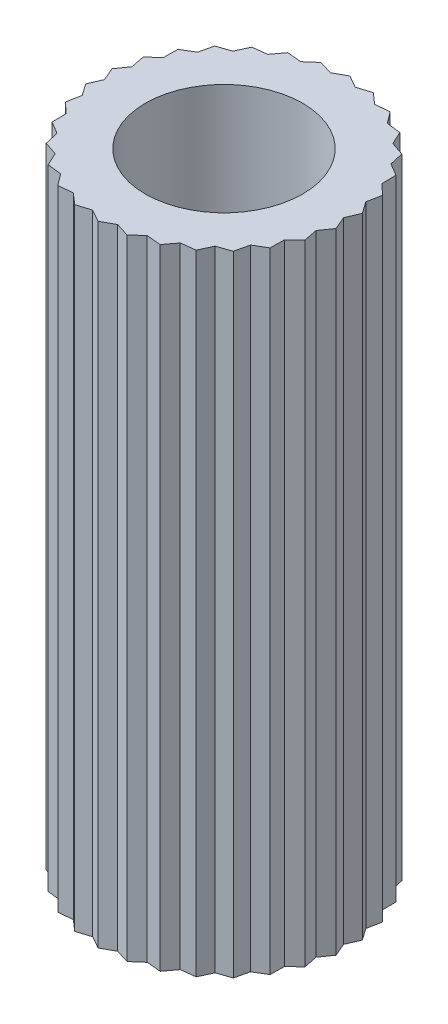
SolidWorks part; units mm, degrees
ref_plane "前视基准面" through (0, 0, 0) normal (0, 0, 1) x (1, 0, 0)
ref_plane "上视基准面" through (0, 0, 0) normal (0, 1, 0) x (1, 0, 0)
ref_plane "右视基准面" through (0, 0, 0) normal (1, 0, 0) x (0, 0, -1)
sketch "草图1" plane through (0, 0, 0) normal (0, 1, 0) x (1, 0, 0)
  line L0 (0, 0) -> (0, 3.1271) construction
  line L1 (0, 1.6) -> (-0.1588, 1.5113)
  line L2 (0, 1.6) -> (0.1588, 1.5113)
  line L3 (0.3327, 1.565) -> (0.1588, 1.5113)
  line L4 (0.3327, 1.565) -> (0.4696, 1.4452)
  line L5 (0.6508, 1.4617) -> (0.4696, 1.4452)
  line L6 (0.6508, 1.4617) -> (0.7598, 1.316)
  line L7 (0.9405, 1.2944) -> (0.7598, 1.316)
  line L8 (0.9405, 1.2944) -> (1.0168, 1.1293)
  line L9 (1.189, 1.0706) -> (1.0168, 1.1293)
  line L10 (1.189, 1.0706) -> (1.2294, 0.8932)
  line L11 (1.3856, 0.8) -> (1.2294, 0.8932)
  line L12 (1.3856, 0.8) -> (1.3882, 0.6181)
  line L13 (1.5217, 0.4944) -> (1.3882, 0.6181)
  line L14 (1.5217, 0.4944) -> (1.4864, 0.3159)
  line L15 (1.5912, 0.1672) -> (1.4864, 0.3159)
  line L16 (1.5912, 0.1672) -> (1.5196, 0)
  line L17 (1.5912, -0.1672) -> (1.5196, 0)
  line L18 (1.5912, -0.1672) -> (1.4864, -0.3159)
  line L19 (1.5217, -0.4944) -> (1.4864, -0.3159)
  line L20 (1.5217, -0.4944) -> (1.3882, -0.6181)
  line L21 (1.3856, -0.8) -> (1.3882, -0.6181)
  line L22 (1.3856, -0.8) -> (1.2294, -0.8932)
  line L23 (1.189, -1.0706) -> (1.2294, -0.8932)
  line L24 (1.189, -1.0706) -> (1.0168, -1.1293)
  line L25 (0.9405, -1.2944) -> (1.0168, -1.1293)
  line L26 (0.9405, -1.2944) -> (0.7598, -1.316)
  line L27 (0.6508, -1.4617) -> (0.7598, -1.316)
  line L28 (0.6508, -1.4617) -> (0.4696, -1.4452)
  line L29 (0.3327, -1.565) -> (0.4696, -1.4452)
  line L30 (0.3327, -1.565) -> (0.1588, -1.5113)
  line L31 (0, -1.6) -> (0.1588, -1.5113)
  line L32 (0, -1.6) -> (-0.1588, -1.5113)
  line L33 (-0.3327, -1.565) -> (-0.1588, -1.5113)
  line L34 (-0.3327, -1.565) -> (-0.4696, -1.4452)
  line L35 (-0.6508, -1.4617) -> (-0.4696, -1.4452)
  line L36 (-0.6508, -1.4617) -> (-0.7598, -1.316)
  line L37 (-0.9405, -1.2944) -> (-0.7598, -1.316)
  line L38 (-0.9405, -1.2944) -> (-1.0168, -1.1293)
  line L39 (-1.189, -1.0706) -> (-1.0168, -1.1293)
  line L40 (-1.189, -1.0706) -> (-1.2294, -0.8932)
  line L41 (-1.3856, -0.8) -> (-1.2294, -0.8932)
  line L42 (-1.3856, -0.8) -> (-1.3882, -0.6181)
  line L43 (-1.5217, -0.4944) -> (-1.3882, -0.6181)
  line L44 (-1.5217, -0.4944) -> (-1.4864, -0.3159)
  line L45 (-1.5912, -0.1672) -> (-1.4864, -0.3159)
  line L46 (-1.5912, -0.1672) -> (-1.5196, 0)
  line L47 (-1.5912, 0.1672) -> (-1.5196, 0)
  line L48 (-1.5912, 0.1672) -> (-1.4864, 0.3159)
  line L49 (-1.5217, 0.4944) -> (-1.4864, 0.3159)
  line L50 (-1.5217, 0.4944) -> (-1.3882, 0.6181)
  line L51 (-1.3856, 0.8) -> (-1.3882, 0.6181)
  line L52 (-1.3856, 0.8) -> (-1.2294, 0.8932)
  line L53 (-1.189, 1.0706) -> (-1.2294, 0.8932)
  line L54 (-1.189, 1.0706) -> (-1.0168, 1.1293)
  line L55 (-0.9405, 1.2944) -> (-1.0168, 1.1293)
  line L56 (-0.9405, 1.2944) -> (-0.7598, 1.316)
  line L57 (-0.6508, 1.4617) -> (-0.7598, 1.316)
  line L58 (-0.6508, 1.4617) -> (-0.4696, 1.4452)
  line L59 (-0.3327, 1.565) -> (-0.4696, 1.4452)
  line L60 (-0.3327, 1.565) -> (-0.1588, 1.5113)
  circle A1 centre (0, 0) radius 1
  dimension "D1" = 1.6
  dimension "D2" = 2
  dimension "D4" = 30
extrude "凸台-拉伸1" add sketch "草图1" along normal blind 8
